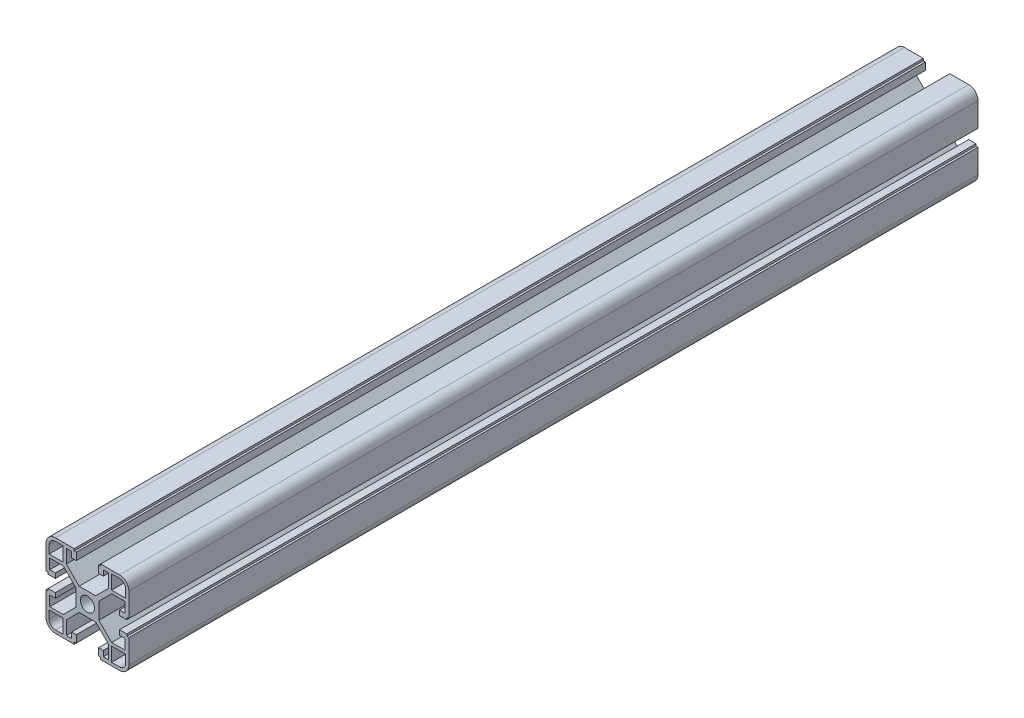
SolidWorks part; units mm, degrees
material "6061-T6 (SS)"
ref_plane "Front Plane" through (0, 0, 0) normal (0, 0, 1) x (1, 0, 0)
ref_plane "Top Plane" through (0, 0, 0) normal (0, 1, 0) x (1, 0, 0)
ref_plane "Right Plane" through (0, 0, 0) normal (1, 0, 0) x (0, 0, -1)
sketch "Sketch1" plane through (0, 0, 0) normal (0, 0, 1) x (1, 0, 0)
  line L0 (3.4, 0) -> (5.5, 0)
  line L1 (10.19, 11.69) -> (4, 5.5)
  line L2 (11.69, 10.19) -> (5.5, 4)
  line L3 (18.2, 10.19) -> (11.69, 10.19)
  line L4 (18.2, 10.19) -> (18.2, 5.2656)
  line L5 (18.2, 5.2656) -> (15.5, 5.2656)
  line L6 (15.5, 5.2656) -> (15.5, 2.9656)
  line L7 (15.5, 2.9656) -> (19, 2.9656)
  line L8 (19, 2.9656) -> (19, 3.9656)
  line L9 (19, 3.9656) -> (20, 3.9656)
  line L10 (20, 3.9656) -> (20, 15.5)
  line L11 (15.5, 20) -> (6.3853, 20)
  line L12 (18.5, 11.69) -> (18.5, 15.5)
  line L13 (15.5, 18.5) -> (11.69, 18.5)
  line L14 (11.69, 11.69) -> (11.69, 18.5)
  line L15 (0, 3.4) -> (0, 5.5)
  line L16 (4, 5.5) -> (0, 5.5)
  line L17 (6.3853, 20) -> (6.3853, 19)
  line L18 (5.5, 0) -> (5.5, 4)
  line L19 (6.3853, 19) -> (5.3853, 19)
  line L20 (5.3853, 19) -> (5.3853, 15.5)
  line L21 (5.3853, 15.5) -> (7.6853, 15.5)
  line L22 (10.19, 11.69) -> (10.19, 18.2)
  line L23 (11.69, 11.69) -> (18.5, 11.69)
  line L24 (7.6853, 18.2) -> (7.6853, 15.5)
  line L25 (10.19, 18.2) -> (7.6853, 18.2)
  arc A0 (20, 15.5) -> (15.5, 20) centre (15.5, 15.5) ccw
  arc A1 (18.5, 15.5) -> (15.5, 18.5) centre (15.5, 15.5) ccw
  arc A2 (3.4, 0) -> (0, 3.4) centre (0, 0) ccw
  dimension "D3" = 4.5
  dimension "D18" = 1.5
  dimension "D9" = 3.4
  dimension "D20" = 1.8
  dimension "D25" = 3
  dimension "D1" = 5.5
  dimension "D2" = 1.5
  dimension "D4" = 14.5
  dimension "D5" = 1.5
  dimension "D6" = 2.1
  dimension "D7" = 2.3
  dimension "D8" = 1.8
  dimension "D10" = 6.81
  dimension "D11" = 2.1
  dimension "D12" = 1
  dimension "D13" = 4.5
  dimension "D14" = 45
  dimension "D15" = 14.5
  dimension "D16" = 1
  dimension "D17" = 1.5
  dimension "D19" = 6.81
  dimension "D21" = 4.5
  dimension "D22" = 2.3
  dimension "D23" = 1
  dimension "D24" = 1
  dimension "D26" = 8.754
  dimension "D27" = 8.754
  dimension "D28" = 4.9244
  dimension "D29" = 2.5047
extrude "Boss-Extrude1" add sketch "Sketch1" along normal blind 410
mirror "Mirror1" about plane through (0, 0, 0) normal (0, 1, 0) of "Boss-Extrude1"
mirror "Mirror2" about plane through (0, 0, 0) normal (1, 0, 0) of "Boss-Extrude1"
mirror "Mirror3" about plane through (0, 0, 0) normal (0, 1, 0) of "Mirror2"
sketch "Croquis2" plane through (0, 0, 410) normal (0, 0, 1) x (1, 0, 0)
  line L0 (-4, 5.5) -> (-5.5, 4)
  line L1 (-5.5, 4) -> (-5.5, -4)
  line L2 (-5.5, -4) -> (-4, -5.5)
  line L3 (-4, -5.5) -> (-4, -28.3763)
  line L4 (-4, -28.3763) -> (-28.3763, -28.3763)
  line L5 (-28.3763, -28.3763) -> (-28.3763, 30.8262)
  line L6 (-28.3763, 30.8262) -> (-4, 30.8262)
  line L7 (-4, 30.8262) -> (-4, 5.5)
extrude "Cortar-Extruir2" [suppressed] cut sketch "Croquis2" against normal blind 70
